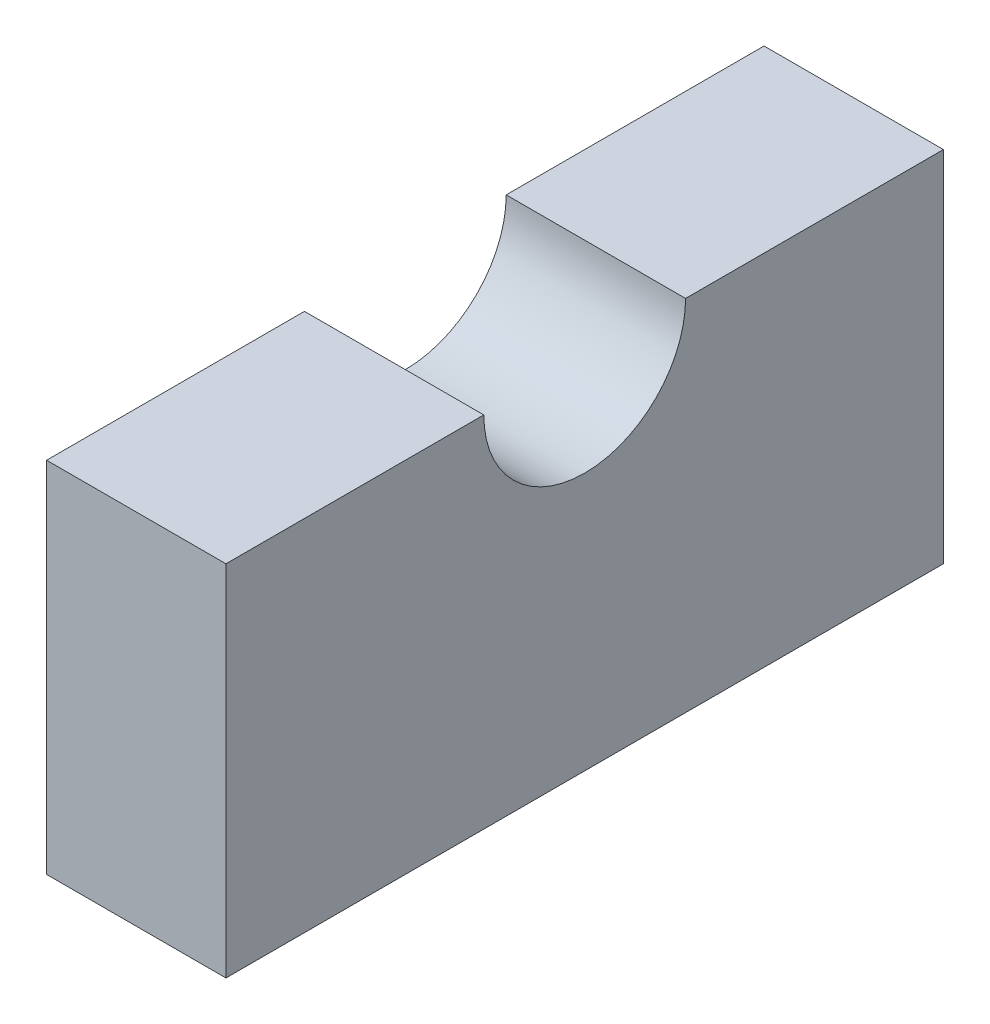
SolidWorks part; units mm, degrees
ref_plane "Front Plane" through (0, 0, 0) normal (0, 0, 1) x (1, 0, 0)
ref_plane "Top Plane" through (0, 0, 0) normal (0, 1, 0) x (1, 0, 0)
ref_plane "Right Plane" through (0, 0, 0) normal (1, 0, 0) x (0, 0, -1)
sketch "Sketch1" plane through (0, 0, 0) normal (1, 0, 0) x (0, 0, -1)
  line L0 (14.2875, 50.8) -> (50.8, 50.8)
  line L1 (-50.8, 0) -> (50.8, 0)
  line L2 (-50.8, 0) -> (-50.8, 50.8)
  line L3 (-50.8, 50.8) -> (-14.2875, 50.8)
  line L4 (50.8, 0) -> (50.8, 50.8)
  arc A0 (-14.2875, 50.8) -> (14.2875, 50.8) centre (0, 50.8) ccw
  point P4 (0, 0)
  point P7 (0, 0)
  dimension "D2" = 14.2875
  dimension "D1" = 101.6
  dimension "D3" = 50.8
  dimension "D4" = 50.8
  dimension "D5" = 50.8
extrude "Boss-Extrude1" add sketch "Sketch1" along normal mid plane 25.4
